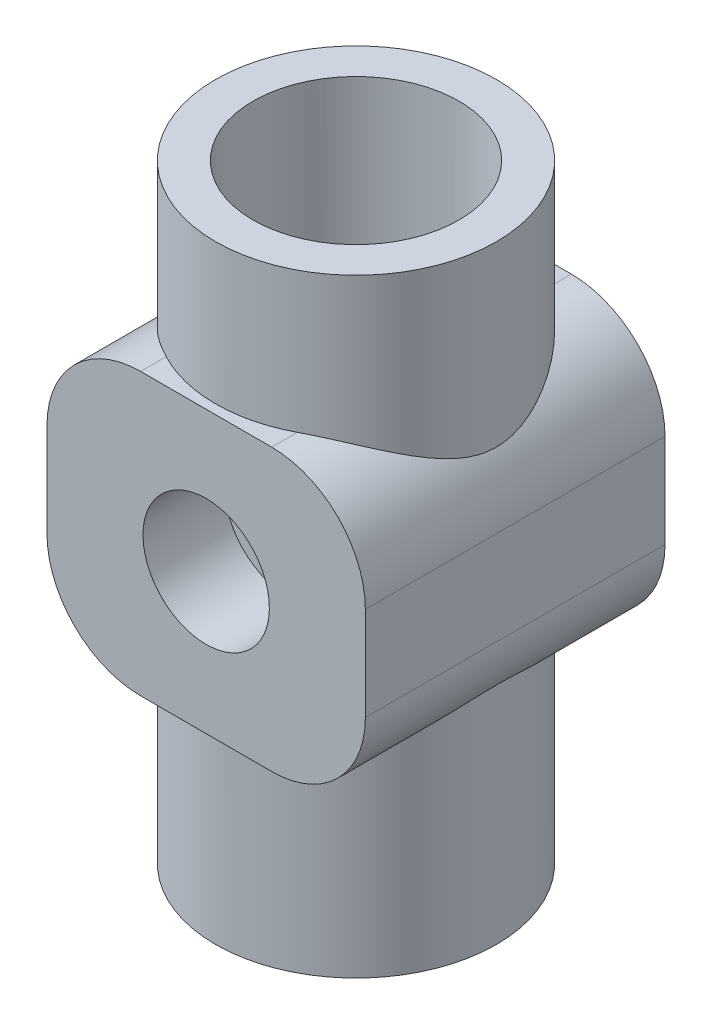
SolidWorks part; units mm, degrees
ref_plane "Front Plane" through (0, 0, 0) normal (0, 0, 1) x (1, 0, 0)
ref_plane "Top Plane" through (0, 0, 0) normal (0, 1, 0) x (1, 0, 0)
ref_plane "Right Plane" through (0, 0, 0) normal (1, 0, 0) x (0, 0, -1)
sketch "Sketch1" plane through (0, 0, 0) normal (0, 0, 1) x (1, 0, 0)
  line L1 (-7, -15) -> (7, -15)
  line L2 (-17, -5) -> (-17, 5)
  line L3 (-7, 15) -> (7, 15)
  line L4 (17, -5) -> (17, 5)
  line L5 (-17, -15) -> (17, 15) construction
  line L6 (-17, 15) -> (17, -15) construction
  arc A0 (7, -15) -> (17, -5) centre (7, -5) ccw
  arc A1 (-7, -15) -> (-17, -5) centre (-7, -5) cw
  arc A2 (7, 15) -> (17, 5) centre (7, 5) cw
  arc A3 (-17, 5) -> (-7, 15) centre (-7, 5) cw
  point P0 (0, 0)
  dimension "D3" = 10
  dimension "D1" = 34
  dimension "D2" = 30
extrude "Boss-Extrude1" add sketch "Sketch1" along normal mid plane 32
sketch "Sketch2" plane through (0, 0, 0) normal (0, 1, 0) x (1, 0, 0)
  line L0 (0, 15) -> (0, 16) construction
  line L3 (7, 16) -> (-7, 16) construction
  circle A0 centre (0, 0) radius 15
  circle A1 centre (0, 0) radius 11
  dimension "D1" = 4
  dimension "D2" = 30
extrude "Boss-Extrude2" add sketch "Sketch2" along normal blind 30 and the other way blind 35
sketch "Sketch3" plane through (0, 0, -16) normal (0, 0, -1) x (-1, 0, 0)
  circle A0 centre (0, 0) radius 6.75
  dimension "D1" = 13.5
extrude "Cut-Extrude1" cut sketch "Sketch3" against normal blind 8.75
mirror "Mirror1" about plane through (0, 0, 0) normal (0, 0, 1) of "Cut-Extrude1"
sketch "Sketch4" plane through (0, 30, 0) normal (0, 1, 0) x (1, 0, 0)
  circle A0 centre (0, 0) radius 11 construction
  circle A1 centre (0, 0) radius 11
extrude "Cut-Extrude2" cut sketch "Sketch4" against normal blind 24
